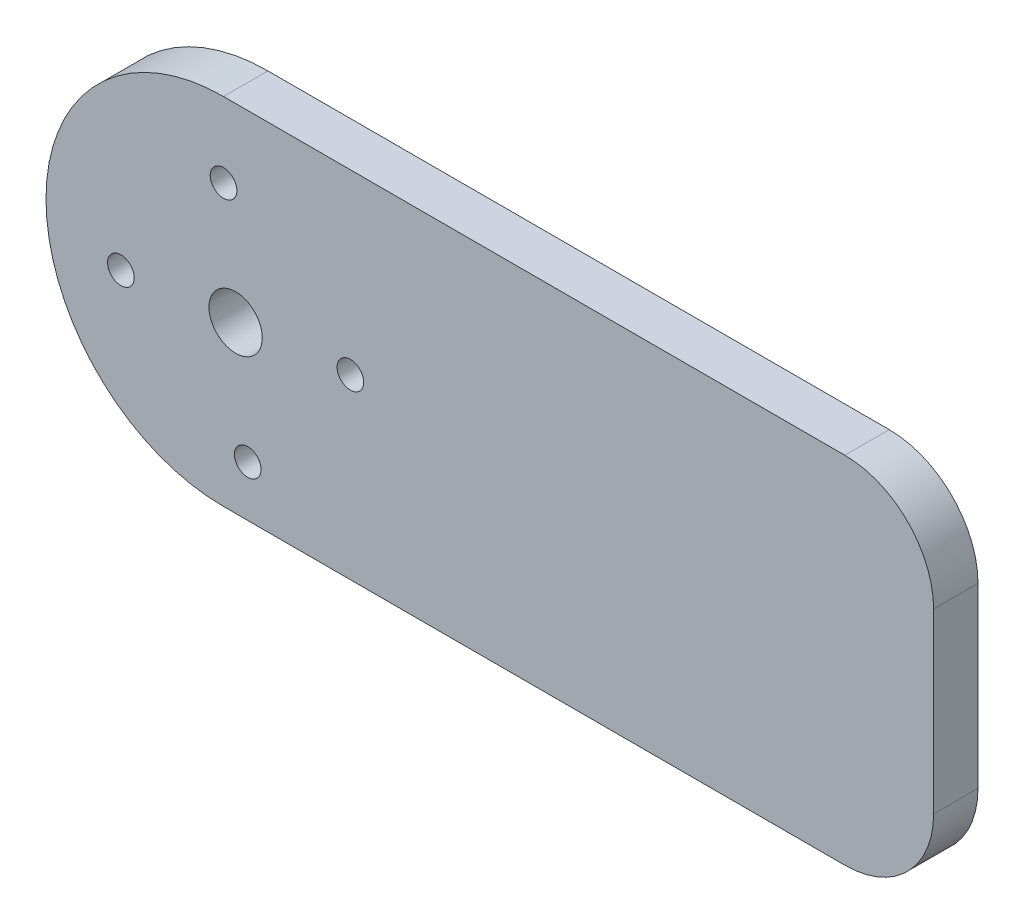
SolidWorks part; units mm, degrees
material "Epoxy, Unfilled"
ref_plane "Front Plane" through (0, 0, 0) normal (0, 0, 1) x (1, 0, 0)
ref_plane "Top Plane" through (0, 0, 0) normal (0, 1, 0) x (1, 0, 0)
ref_plane "Right Plane" through (0, 0, 0) normal (1, 0, 0) x (0, 0, -1)
sketch "Sketch1" plane through (0, 0, 0) normal (0, 0, 1) x (1, 0, 0)
  line L0 (0, 0) -> (80, 0) construction
  line L1 (0, 20) -> (80, 20)
  line L2 (0, -20) -> (80, -20)
  line L3 (80, 20) -> (80, -20)
  arc A0 (0, 20) -> (0, -20) centre (0, 0) ccw
  point P3 (40, 0)
  circle B0 centre (0, 11.5645) radius 1.5
  circle B1 centre (14.2921, 0) radius 1.5
  circle B2 centre (2.7276, -14.2921) radius 1.5
  circle B3 centre (-11.5645, -2.7276) radius 1.5
  dimension "D2" = 20
  dimension "D1" = 80
sketch_block_instance "mounting connector-1"
sketch_block "mounting connector" parameters "D1"=3
extrude "Boss-Extrude1" add sketch "Sketch1" along normal blind 5
sketch "Sketch2" plane through (0, 0, 0) normal (0, 0, -1) x (-1, 0, 0)
  circle A0 centre (-1.3638, -1.3638) radius 3 construction
  circle A1 centre (-1.3638, -1.3638) radius 3
extrude "Cut-Extrude1" cut sketch "Sketch2" against normal blind 10
fillet "Fillet1" radius 10 2 edges at (80, -20, 2.5) (80, 20, 2.5)
